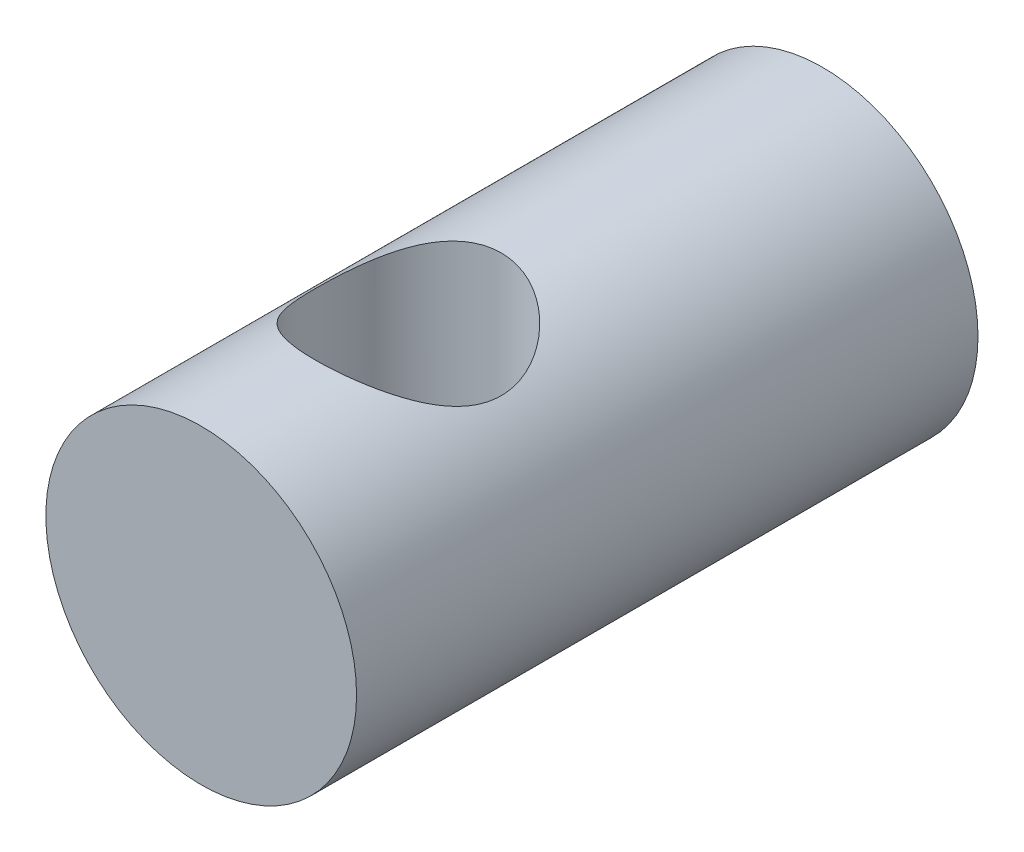
SolidWorks part; units mm, degrees
ref_plane "Front Plane" through (0, 0, 0) normal (0, 0, 1) x (1, 0, 0)
ref_plane "Top Plane" through (0, 0, 0) normal (0, 1, 0) x (1, 0, 0)
ref_plane "Right Plane" through (0, 0, 0) normal (1, 0, 0) x (0, 0, -1)
sketch "Sketch1" plane through (0, 0, 0) normal (0, 0, 1) x (1, 0, 0)
  circle A0 centre (0, 0) radius 3.175
  dimension "D1" = 6.35
extrude "Boss-Extrude1" add sketch "Sketch1" along normal blind 12.7
ref_plane "Plane1" through (0, 0, 8.4667) normal (0, 0, 1) x (1, 0, 0)
hole_wizard "#10-24 Tapped Hole2" positions "3DSketch1" profile "Sketch6" tap size "#10-24" standard "ANSI Inch" end condition through all
sketch3d "3DSketch1"
  point P0 (0, 3.175, 8.4667)
sketch "Sketch6" plane through (0, 3.175, 8.4667) normal (1, 0, 0) x (0, 0, 1)
  line L0 (0, 0) -> (0, 6.35)
  line L1 (0, 6.35) -> (1.8986, 6.35)
  line L2 (1.8986, 6.35) -> (1.8986, 0)
  line L5 (1.8986, 0) -> (0, 0)
  line L11 (0, -6.35) -> (0, 107.95) construction
  dimension "Thru Tap Drill Dia." = 3.7973
  dimension "Thru Tap Drill Depth" = 6.35
cosmetic thread "Hole Thread2" parameters "D2"=4.826
